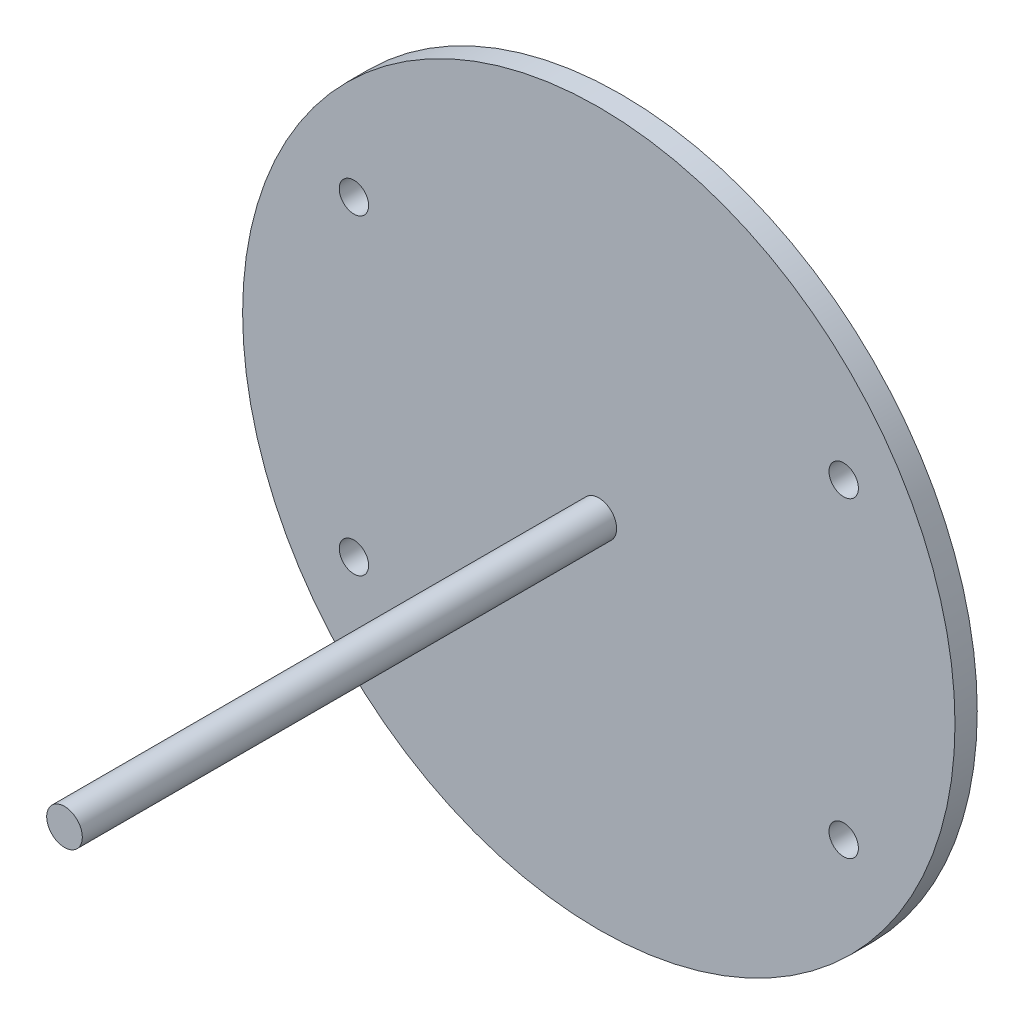
SolidWorks part; units mm, degrees
ref_plane "前视基准面" through (0, 0, 0) normal (0, 0, 1) x (1, 0, 0)
ref_plane "上视基准面" through (0, 0, 0) normal (0, 1, 0) x (1, 0, 0)
ref_plane "右视基准面" through (0, 0, 0) normal (1, 0, 0) x (0, 0, -1)
sketch "草图1" plane through (0, 0, 0) normal (0, 0, 1) x (1, 0, 0)
  line L1 (-27.5, -17.5) -> (27.5, -17.5) construction
  line L2 (-27.5, -17.5) -> (-27.5, 17.5) construction
  line L3 (-27.5, 17.5) -> (27.5, 17.5) construction
  line L4 (27.5, -17.5) -> (27.5, 17.5) construction
  line L5 (-27.5, -17.5) -> (27.5, 17.5) construction
  line L6 (-27.5, 17.5) -> (27.5, -17.5) construction
  circle A0 centre (0, 0) radius 40
  circle A1 centre (-27.5, 17.5) radius 1.65
  circle A2 centre (27.5, 17.5) radius 1.65
  circle A3 centre (27.5, -17.5) radius 1.65
  circle A4 centre (-27.5, -17.5) radius 1.65
  dimension "D1" = 80
  dimension "D2" = 3.3
  dimension "D3" = 55
  dimension "D4" = 35
extrude "凸台-拉伸1" add sketch "草图1" along normal blind 2.5
sketch "草图2" plane through (0, 0, 2.5) normal (0, 0, 1) x (1, 0, 0)
  circle A0 centre (0, 0) radius 2
  dimension "D1" = 4
extrude "凸台-拉伸2" add sketch "草图2" along normal blind 60
